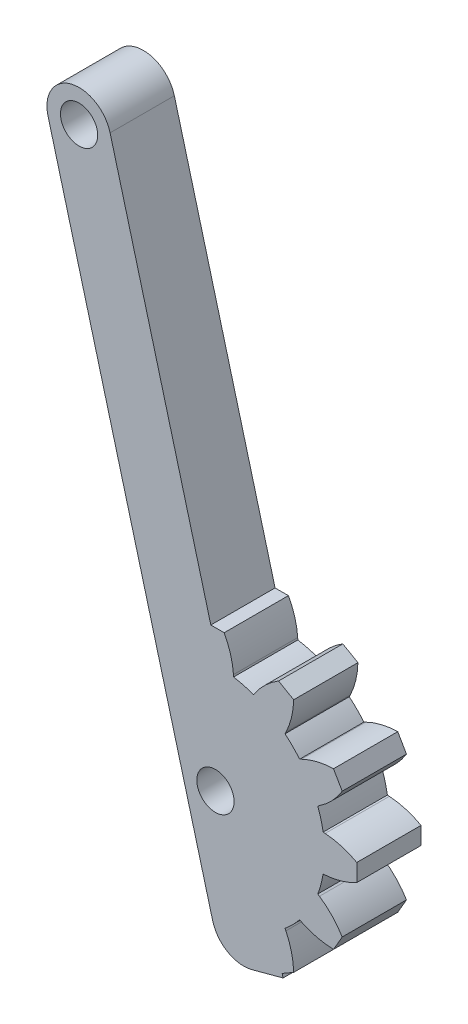
SolidWorks part; units mm, degrees
ref_plane "Front Plane" through (0, 0, 0) normal (0, 0, 1) x (1, 0, 0)
ref_plane "Top Plane" through (0, 0, 0) normal (0, 1, 0) x (1, 0, 0)
ref_plane "Right Plane" through (0, 0, 0) normal (1, 0, 0) x (0, 0, -1)
ref_plane "Plane1" through (0, 0, 1.9) normal (0, 0, 1) x (1, 0, 0)
sketch "Sketch1" plane through (0, 0, 1.9) normal (0, 0, 1) x (1, 0, 0)
  line L0 (-13.0264, 38.9559) -> (-0.2149, -8.8574)
  line L1 (2.847, -10.6252) -> (5.2618, -9.9781)
  line L2 (5.2618, -9.9781) -> (5.1889, -9.7059)
  line L3 (5.1889, -9.7059) -> (6.0876, -9.187)
  line L4 (5.4819, -6.6916) -> (5.4141, -6.5527)
  line L5 (6.5527, -5.4141) -> (6.6916, -5.4819)
  line L6 (9.187, -6.0876) -> (9.8655, -4.9124)
  line L7 (8.0933, -3.0542) -> (7.9651, -2.9677)
  line L8 (8.3818, -1.4124) -> (8.5361, -1.4016)
  line L9 (11, -0.6785) -> (11, 0.6785)
  line L10 (8.5361, 1.4016) -> (8.3818, 1.4124)
  line L11 (7.9651, 2.9677) -> (8.0933, 3.0542)
  line L12 (9.8655, 4.9124) -> (9.187, 6.0876)
  line L13 (6.6916, 5.4819) -> (6.5527, 5.4141)
  line L14 (5.4141, 6.5527) -> (5.4819, 6.6916)
  line L15 (6.0876, 9.187) -> (4.9124, 9.8655)
  line L16 (3.0542, 8.0933) -> (2.9677, 7.9651)
  line L17 (1.4124, 8.3818) -> (1.4016, 8.5361)
  line L18 (0.6785, 11) -> (-0.3593, 11)
  line L19 (-0.3593, 11) -> (-8.1968, 40.25)
  line L20 (0, 0) -> (-10.6116, 39.603) construction
  circle A0 centre (-10.6116, 39.603) radius 1.45
  arc A1 (-0.2149, -8.8574) -> (2.847, -10.6252) centre (2.2, -8.2104) ccw
  arc A2 (6.0876, -9.187) -> (5.4819, -6.6916) centre (0.0891, -9.3218) ccw
  arc A3 (5.4141, -6.5527) -> (6.5527, -5.4141) centre (0, 0) ccw
  arc A4 (6.6916, -5.4819) -> (9.187, -6.0876) centre (9.3218, -0.0891) ccw
  arc A5 (9.8655, -4.9124) -> (8.0933, -3.0542) centre (4.7381, -8.0284) ccw
  arc A6 (7.9651, -2.9677) -> (8.3818, -1.4124) centre (0, 0) ccw
  arc A7 (8.5361, -1.4016) -> (11, -0.6785) centre (8.1175, 4.5837) ccw
  arc A8 (11, 0.6785) -> (8.5361, 1.4016) centre (8.1175, -4.5837) ccw
  arc A9 (8.3818, 1.4124) -> (7.9651, 2.9677) centre (0, 0) ccw
  arc A10 (8.0933, 3.0542) -> (9.8655, 4.9124) centre (4.7381, 8.0284) ccw
  arc A11 (9.187, 6.0876) -> (6.6916, 5.4819) centre (9.3218, 0.0891) ccw
  arc A12 (6.5527, 5.4141) -> (5.4141, 6.5527) centre (0, 0) ccw
  arc A13 (5.4819, 6.6916) -> (6.0876, 9.187) centre (0.0891, 9.3218) ccw
  arc A14 (4.9124, 9.8655) -> (3.0542, 8.0933) centre (8.0284, 4.7381) ccw
  arc A15 (2.9677, 7.9651) -> (1.4124, 8.3818) centre (0, 0) ccw
  arc A16 (1.4016, 8.5361) -> (0.6785, 11) centre (-4.5837, 8.1175) ccw
  arc A17 (-8.1968, 40.25) -> (-13.0264, 38.9559) centre (-10.6116, 39.603) ccw
  circle A18 centre (0, 0) radius 1.45
  dimension "D1" = 2.9
  dimension "D3" = 0.0891
  dimension "D4" = 8.5
  dimension "D5" = 6
  dimension "D20" = 2.9
  dimension "D6" = 0.6785
  dimension "D7" = 1.4016
  dimension "D8" = 1.4124
  dimension "D9" = 2.2
  dimension "D10" = 2.847
  dimension "D11" = 2.9677
  dimension "D12" = 3.0542
  dimension "D13" = 4.7381
  dimension "D14" = 4.9124
  dimension "D15" = 5.1889
  dimension "D16" = 5.4141
  dimension "D17" = 6.5527
  dimension "D18" = 8.1175
  dimension "39" = 41
extrude "Boss-Extrude1" add sketch "Sketch1" against normal blind 5
